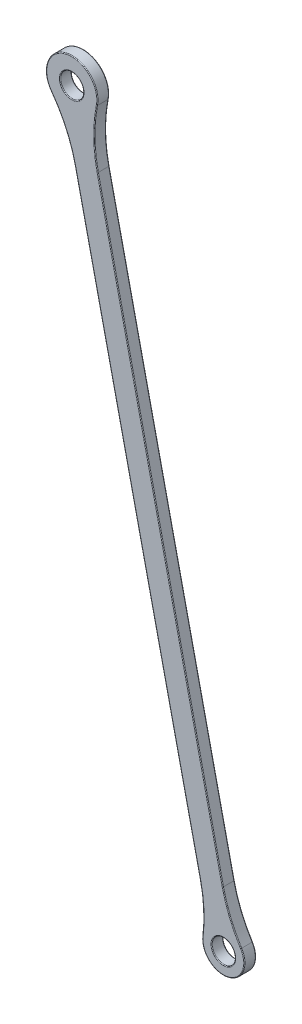
SolidWorks part; units mm, degrees
ref_plane "Front Plane" through (0, 0, 0) normal (0, 0, 1) x (1, 0, 0)
ref_plane "Top Plane" through (0, 0, 0) normal (0, 1, 0) x (1, 0, 0)
ref_plane "Right Plane" through (0, 0, 0) normal (1, 0, 0) x (0, 0, -1)
sketch "Sketch1" plane through (0, 0, 0) normal (0, 0, 1) x (1, 0, 0)
  line L0 (14.5, 81.5) -> (-17.9832, 225.8913) construction
  line L1 (14.5, 81.5) -> (-17.9832, 225.8913) construction
  line L2 (14.5, 81.5) -> (-17.9832, 225.8913) construction
  line L3 (12.061, 80.9513) -> (-20.4223, 225.3426)
  line L4 (16.939, 82.0487) -> (-15.5442, 226.44)
  arc A0 (-14.469, 221.6604) -> (-19.3471, 220.563) centre (-17.9832, 225.8913) ccw
  arc A1 (11.2397, 84.6017) -> (16.1178, 85.6991) centre (14.5, 81.5) ccw
  arc A2 (12.061, 80.9513) -> (16.939, 82.0487) centre (14.5, 81.5) ccw
  arc A3 (-15.5442, 226.44) -> (-20.4223, 225.3426) centre (-17.9832, 225.8913) ccw
  arc A4 (-20.4223, 225.3426) -> (-15.5442, 226.44) centre (-17.9832, 225.8913) ccw
  arc A5 (12.061, 80.9513) -> (16.939, 82.0487) centre (14.5, 81.5) cw
  point P5 (-1.7416, 153.6956)
  dimension "D1" = 11
  dimension "D2" = 9
  dimension "D3" = 5
extrude "Boss-Extrude1" add sketch "Sketch1" against normal blind 2.5 contours L3 A5 L4 A4 | A3 L4 A0 L3 | A2 L3 A1 L4
fillet "Fillet1" radius 30 4 edges at (-14.469, 221.6604, -1.25) (-19.3471, 220.563, -1.25) (11.2397, 84.6017, -1.25) (16.1178, 85.6991, -1.25)
fillet "Fillet2" radius 0.15 20 edges at (17, 81.5, -2.5) (17, 81.5, 0) (-15.4832, 225.8913, -2.5) (-15.4832, 225.8913, 0) (15.9467, 88.4554, -2.5) (15.9467, 88.4554, 0) (0.9945, 152.9238, -2.5) (0.9945, 152.9238, 0) (-13.1378, 218.6623, -2.5) (-13.1378, 218.6623, 0) (-19.1904, 231.2572, 0) (-19.1904, 231.2572, -2.5) (-19.266, 217.2837, -2.5) (-19.266, 217.2837, 0) (-3.8836, 151.8264, 0) (-3.8836, 151.8264, -2.5) (10.214, 87.1657, -2.5) (10.214, 87.1657, 0) (15.4877, 77.1097, 0) (15.4877, 77.1097, -2.5)
